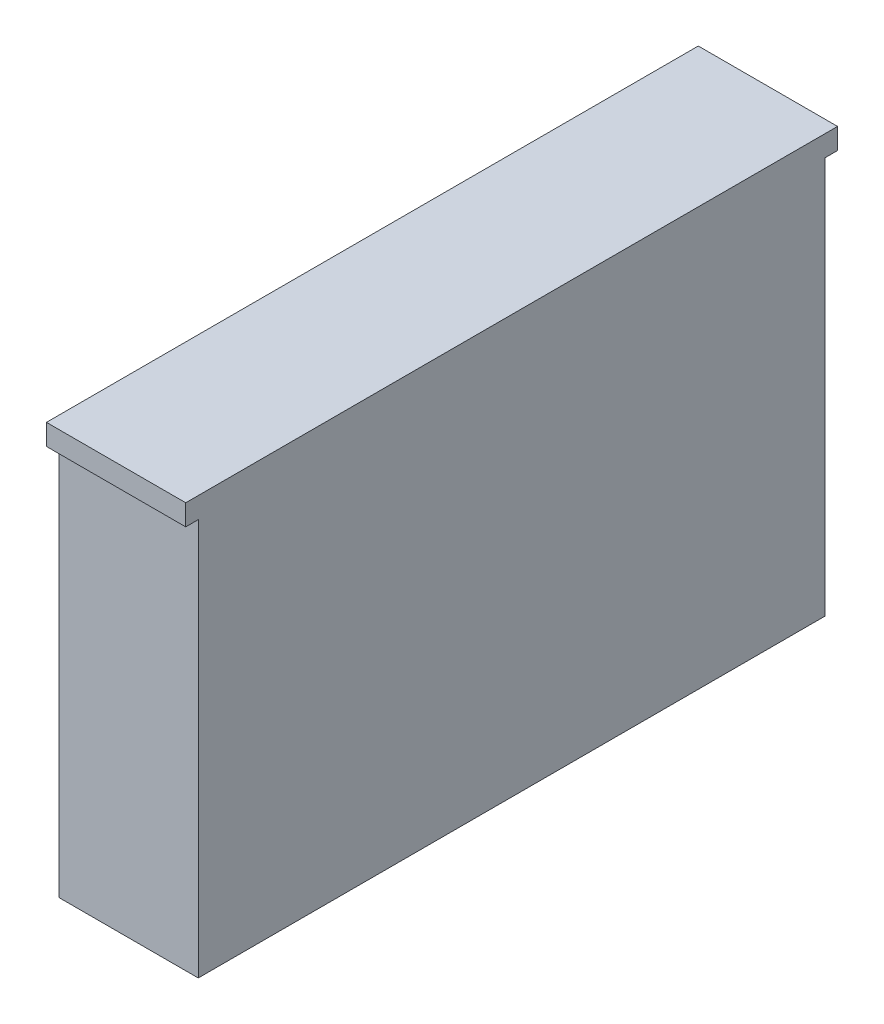
SolidWorks part; units mm, degrees
ref_plane "Alzado" through (0, 0, 0) normal (0, 0, 1) x (1, 0, 0)
ref_plane "Planta" through (0, 0, 0) normal (0, 1, 0) x (1, 0, 0)
ref_plane "Vista lateral" through (0, 0, 0) normal (1, 0, 0) x (0, 0, -1)
sketch "Croquis2" plane through (0, 0, 0) normal (1, 0, 0) x (0, 0, -1)
  line L1 (225, -150) -> (-225, -150)
  line L2 (225, -150) -> (225, 150)
  line L3 (225, 150) -> (-225, 150)
  line L4 (-225, -150) -> (-225, 150)
  line L5 (225, -150) -> (-225, 150) construction
  line L6 (225, 150) -> (-225, -150) construction
  point P0 (0, 0)
  dimension "D1" = 300
  dimension "D2" = 450
extrude "Saliente-Extruir1" add sketch "Croquis2" along normal blind 100
sketch "Croquis3" plane through (0, 0, 0) normal (-1, 0, 0) x (0, 0, 1)
  line L0 (-85.1737, 98.5116) -> (-2.5894, 8.4513) construction
  line L1 (-822.5697, 83.8671) -> (1.4303, 83.8671) construction
sketch "Croquis4" plane through (0, 0, -225) normal (0, 0, -1) x (-1, 0, 0)
  line L0 (-100, 150) -> (0, 150) construction
  line L5 (-100, 150) -> (0, 150)
  line L6 (0, 150) -> (0, 135)
  line L7 (0, -150) -> (0, 150) construction
  line L8 (0, 135) -> (-100, 135)
  line L9 (-100, -150) -> (-100, 150) construction
  line L10 (-100, 135) -> (-100, 150)
  point P0 (-79.3167, 150)
  dimension "D1" = 15
extrude "Saliente-Extruir2" add sketch "Croquis4" along normal blind 9
sketch "Croquis5" plane through (0, 0, 225) normal (0, 0, 1) x (1, 0, 0)
  line L1 (0, 150) -> (100, 150)
  line L2 (100, 150) -> (100, 135)
  line L3 (100, 135) -> (0, 135)
  line L4 (0, 135) -> (0, 150)
extrude "Saliente-Extruir3" add sketch "Croquis5" along normal blind 9
sketch "Croquis6" plane through (0, 0, -225) normal (0, 0, -1) x (-1, 0, 0)
  line L0 (-45.7416, -114.9273) -> (182.2584, -114.9273) construction
sketch "Croquis7" plane through (0, 0, -225) normal (0, 0, -1) x (-1, 0, 0)
  line L0 (-17.8265, -149.264) -> (210.1735, -149.264) construction
  line L1 (-208.937, -73.3363) -> (-75.6037, -73.3363) construction
sketch "Croquis8" plane through (0, -150, 0) normal (0, -1, 0) x (1, 0, 0)
  line L0 (-86.3236, 82.273) -> (47.0097, 82.273) construction
sketch "Croquis9" plane through (0, 0, 0) normal (-1, 0, 0) x (0, 0, 1)
  line L0 (-99.6421, -23.8204) -> (-52.3088, -23.8204) construction
sketch "Croquis10" plane through (0, 0, 0) normal (-1, 0, 0) x (0, 0, 1)
  line L0 (-79.3698, -143.6865) -> (-50.0365, -143.6865) construction
  line L1 (-79.5365, 75.9615) -> (-50.8698, 75.9615) construction
  line L2 (18.9393, -6.6427) -> (68.2726, -6.6427) construction
